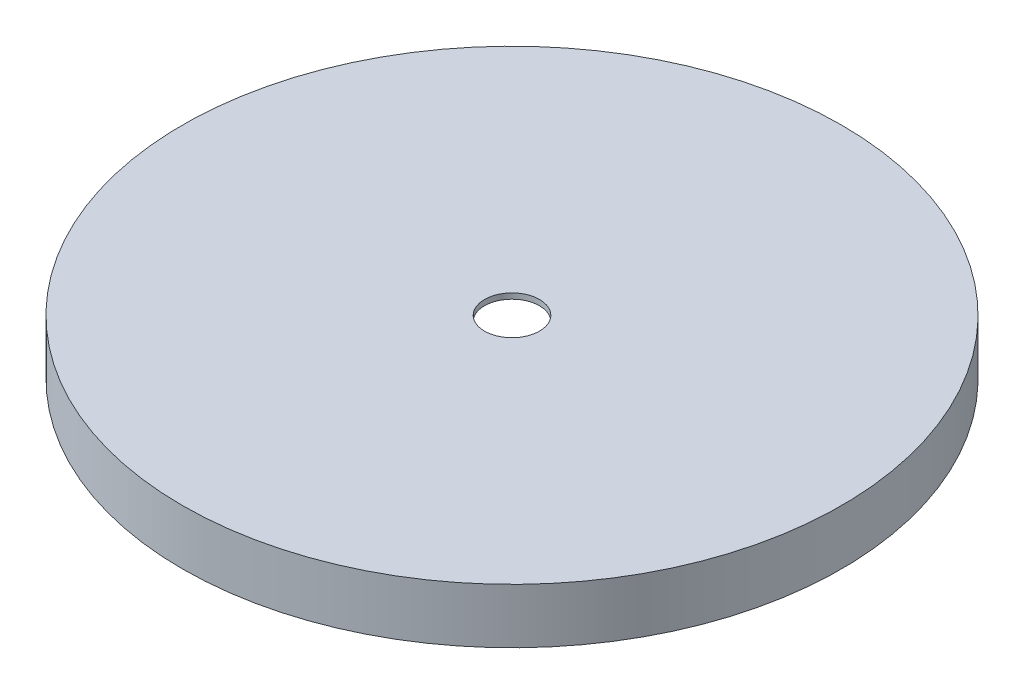
SolidWorks part; units mm, degrees
material "PE High Density"
ref_plane "Front Plane" through (0, 0, 0) normal (0, 0, 1) x (1, 0, 0)
ref_plane "Top Plane" through (0, 0, 0) normal (0, 1, 0) x (1, 0, 0)
ref_plane "Right Plane" through (0, 0, 0) normal (1, 0, 0) x (0, 0, -1)
sketch "Sketch1" plane through (0, 0, 0) normal (0, 0, 1) x (1, 0, 0)
  line L0 (0, 0) -> (0, 25.4)
  line L1 (0, 25.4) -> (152.4, 25.4)
  line L2 (152.4, 25.4) -> (152.4, 0)
  line L3 (152.4, 0) -> (0, 0)
  dimension "D1" = 152.4
  dimension "D2" = 152.4
  dimension "D3" = 25.4
revolve "Revolve1" add sketch "Sketch1" angle 360 about L0
shell "Shell2" thickness 2.54
sketch "Sketch2" plane through (0, 25.4, 0) normal (0, 1, 0) x (1, 0, 0)
  circle A0 centre (0, 0) radius 12.7
  dimension "D1" = 25.4
extrude "Cut-Extrude1" cut sketch "Sketch2" against normal through all
